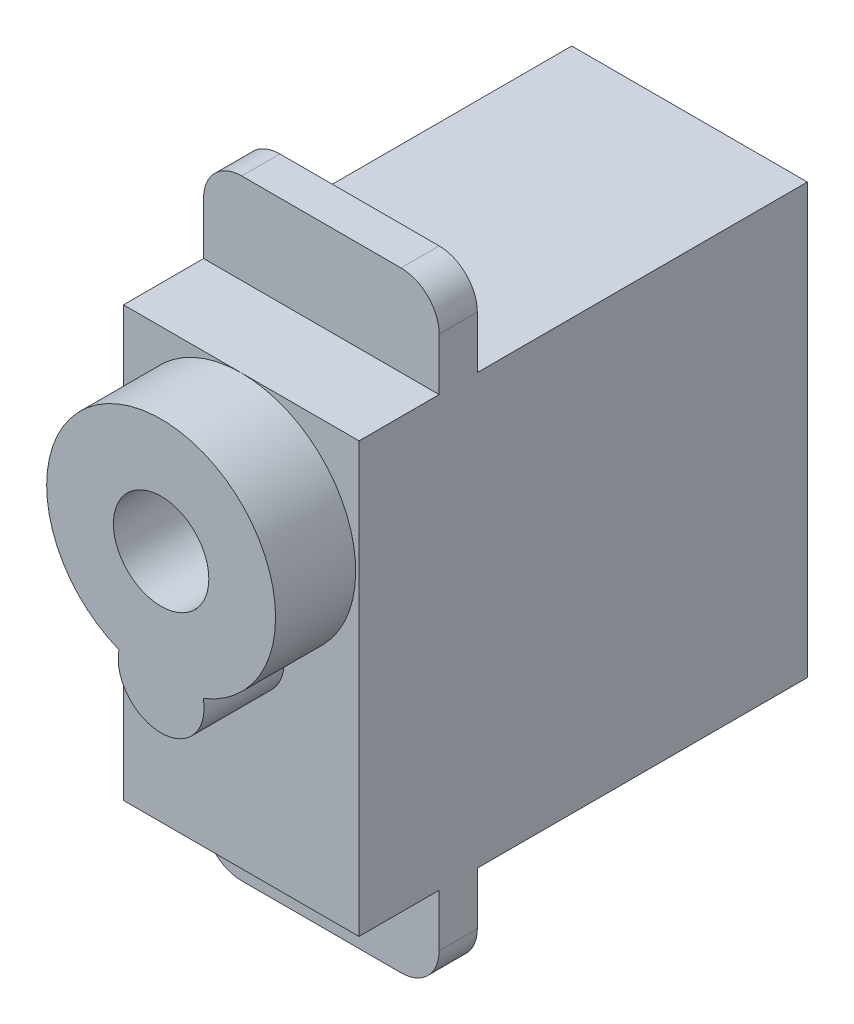
SolidWorks part; units mm, degrees
ref_plane "Front Plane" through (0, 0, 0) normal (0, 0, 1) x (1, 0, 0)
ref_plane "Top Plane" through (0, 0, 0) normal (0, 1, 0) x (1, 0, 0)
ref_plane "Right Plane" through (0, 0, 0) normal (1, 0, 0) x (0, 0, -1)
sketch "Sketch3" plane through (0, -28.2755, 0) normal (1, 0, 0) x (0, 1, 0)
  line L1 (35.8597, 178.8667) -> (13.3597, 178.8667)
  line L2 (35.8597, 178.8667) -> (35.8597, 155.3667)
  line L3 (35.8597, 155.3667) -> (13.3597, 155.3667)
  line L4 (13.3597, 178.8667) -> (13.3597, 155.3667)
  dimension "D1" = 22.5
  dimension "D2" = 23.5
extrude "Boss-Extrude1" add sketch "Sketch3" along normal mid plane 12.35
ref_plane "Plane1" through (0, 0, 174.6667) normal (0, 0, 1) x (1, 0, 0)
sketch "Sketch4" plane through (0, 0, 174.6667) normal (0, 0, 1) x (1, 0, 0)
  line L0 (-6.175, 7.5842) -> (-6.175, -14.9158) construction
  line L1 (-6.175, 12.3342) -> (6.175, 12.3342)
  line L2 (-6.175, 12.3342) -> (-6.175, -19.6658)
  line L3 (-6.175, -19.6658) -> (6.175, -19.6658)
  line L4 (6.175, 12.3342) -> (6.175, -19.6658)
  line L5 (6.175, 7.5842) -> (6.175, -14.9158) construction
  line L6 (0, 7.5842) -> (0, -14.9158) construction
  line L7 (6.175, 7.5842) -> (-6.175, 7.5842) construction
  line L8 (6.175, -14.9158) -> (-6.175, -14.9158) construction
  line L9 (0, -3.6658) -> (2.6217, -3.6658) construction
  dimension "D1" = 0
  dimension "D2" = 0
  dimension "D3" = 32
  dimension "D4" = 16
extrude "Boss-Extrude2" add sketch "Sketch4" against normal blind 2
sketch "Sketch5" plane through (0, 0, 178.8667) normal (0, 0, 1) x (1, 0, 0)
  line L0 (6.175, 7.5842) -> (-6.175, 7.5842) construction
  arc A0 (2.2101, -3.9939) -> (-2.2101, -3.9939) centre (0, 1.5842) ccw
  arc A1 (-2.2101, -3.9939) -> (2.2101, -3.9939) centre (0, -4.4158) ccw
  dimension "D1" = 12
  dimension "D2" = 6
  dimension "D3" = 4.5
extrude "Boss-Extrude3" add sketch "Sketch5" along normal blind 4.2
sketch "Sketch6" plane through (0, 0, 183.0667) normal (0, 0, 1) x (1, 0, 0)
  circle A0 centre (0, 1.5842) radius 2.5
  dimension "D1" = 5
extrude "Cut-Extrude1" cut sketch "Sketch6" against normal blind 4.2
fillet "Fillet1" radius 2 4 edges at (6.175, -19.6658, 173.6667) (-6.175, -19.6658, 173.6667) (6.175, 12.3342, 173.6667) (-6.175, 12.3342, 173.6667)
